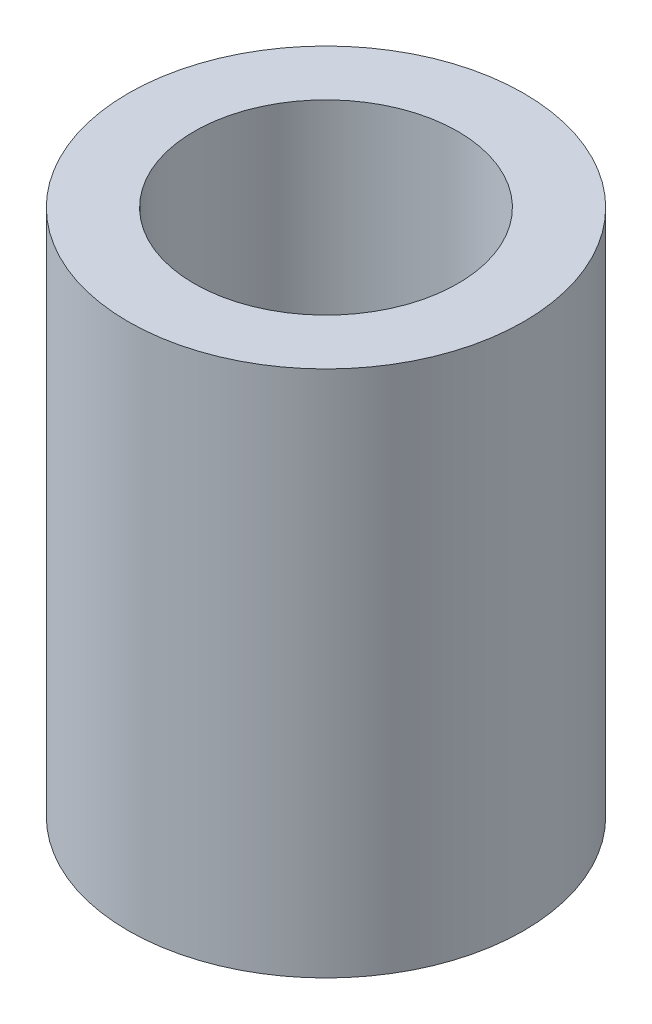
SolidWorks part; units mm, degrees
ref_plane "Front Plane" through (0, 0, 0) normal (0, 0, 1) x (1, 0, 0)
ref_plane "Top Plane" through (0, 0, 0) normal (0, 1, 0) x (1, 0, 0)
ref_plane "Right Plane" through (0, 0, 0) normal (1, 0, 0) x (0, 0, -1)
sketch "Sketch1" plane through (0, 0, 0) normal (0, 1, 0) x (1, 0, 0)
  circle A0 centre (0, 0) radius 6
  circle A1 centre (0, 0) radius 4
  dimension "D1" = 8
  dimension "D2" = 12
extrude "Boss-Extrude1" add sketch "Sketch1" along normal blind 16
